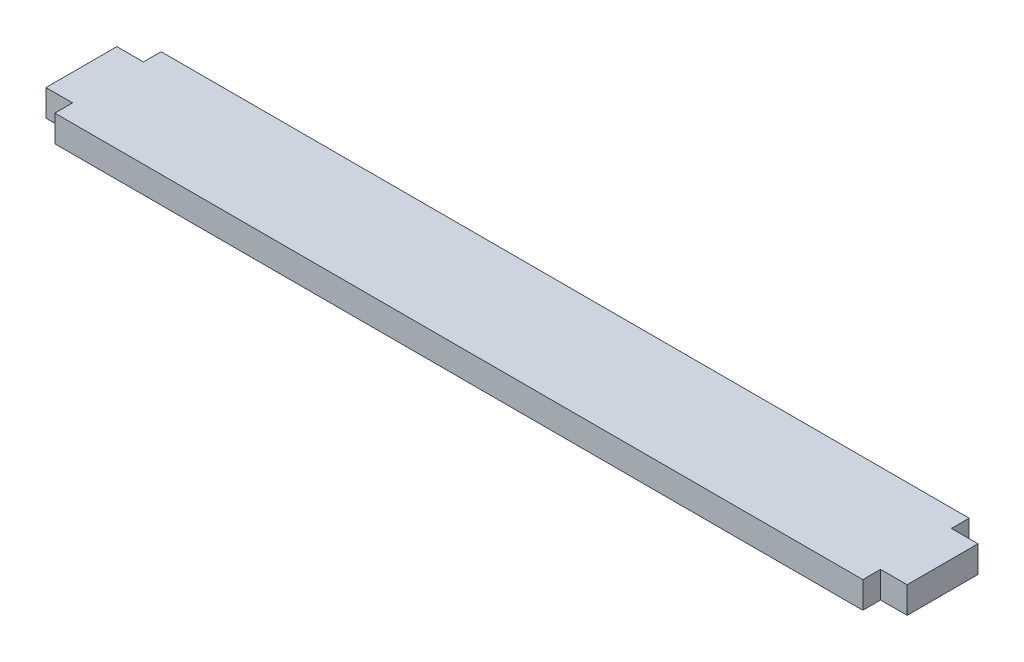
SolidWorks part; units mm, degrees
material "Beech"
ref_plane "Front Plane" through (0, 0, 0) normal (0, 0, 1) x (1, 0, 0)
ref_plane "Top Plane" through (0, 0, 0) normal (0, 1, 0) x (1, 0, 0)
ref_plane "Right Plane" through (0, 0, 0) normal (1, 0, 0) x (0, 0, -1)
sketch "Sketch1" plane through (0, 0, 0) normal (0, 1, 0) x (1, 0, 0)
  line L0 (-45.6, 6) -> (-45.6, 4)
  line L1 (-45.6, -6) -> (45.6, -6)
  line L2 (-45.6, -6) -> (-45.6, 6) construction
  line L3 (-45.6, 6) -> (45.6, 6)
  line L4 (45.6, -6) -> (45.6, 6) construction
  line L5 (-45.6, -6) -> (45.6, 6) construction
  line L6 (-45.6, 6) -> (45.6, -6) construction
  line L7 (-45.6, 4) -> (-48.6, 4)
  line L8 (-48.6, 4) -> (-48.6, -4)
  line L9 (-48.6, -4) -> (-45.6, -4)
  line L10 (-45.6, -4) -> (-45.6, -6)
  line L11 (45.6, 6) -> (45.6, 4)
  line L12 (45.6, 4) -> (48.6, 4)
  line L13 (48.6, 4) -> (48.6, -4)
  line L14 (48.6, -4) -> (45.6, -4)
  line L15 (45.6, -4) -> (45.6, -6)
  point P0 (0, 0)
  dimension "D1" = 91.2
  dimension "D2" = 12
  dimension "D3" = 3
  dimension "D4" = 3
  dimension "D5" = 8
extrude "Boss-Extrude1" add sketch "Sketch1" along normal blind 3
